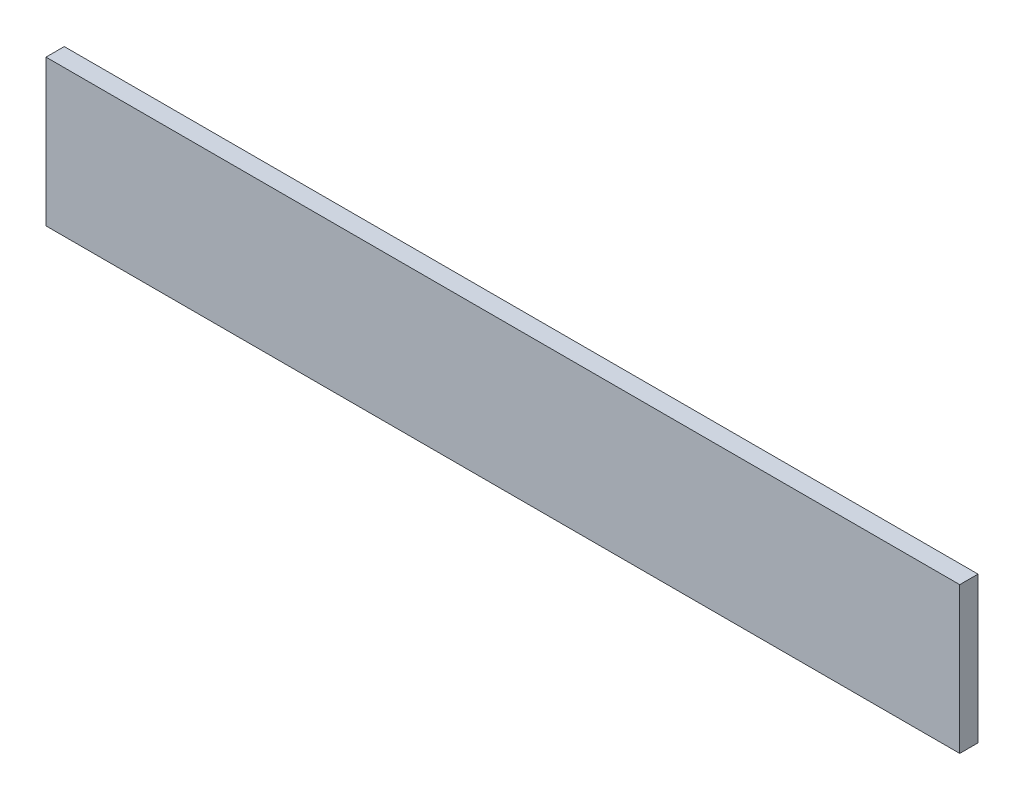
SolidWorks part; units mm, degrees
ref_plane "Plan de face" through (0, 0, 0) normal (0, 0, 1) x (1, 0, 0)
ref_plane "Plan de dessus" through (0, 0, 0) normal (0, 1, 0) x (1, 0, 0)
ref_plane "Plan de droite" through (0, 0, 0) normal (1, 0, 0) x (0, 0, -1)
sketch "Esquisse1" plane through (0, 0, 0) normal (0, 0, 1) x (1, 0, 0)
  line L1 (0, 0) -> (-250, 0)
  line L2 (0, 0) -> (0, 40)
  line L3 (0, 40) -> (-250, 40)
  line L4 (-250, 0) -> (-250, 40)
  dimension "D1" = 250
  dimension "D2" = 40
extrude "Boss.-Extru.1" add sketch "Esquisse1" along normal blind 5
